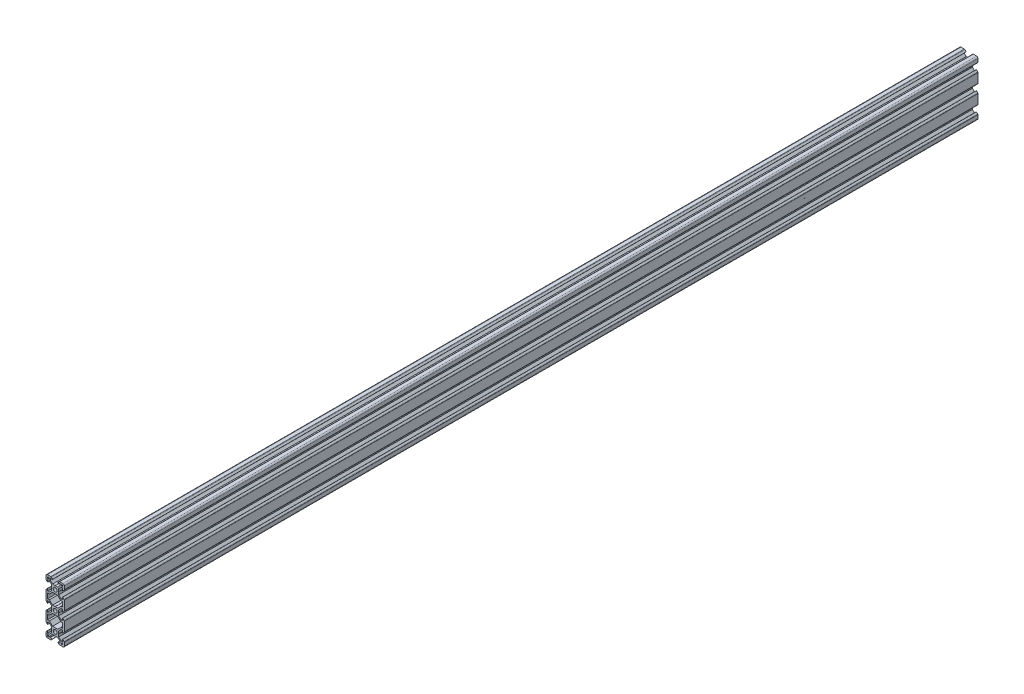
SolidWorks part; units mm, degrees
ref_plane "Front Plane" through (0, 0, 0) normal (0, 0, 1) x (1, 0, 0)
ref_plane "Top Plane" through (0, 0, 0) normal (0, 1, 0) x (1, 0, 0)
ref_plane "Right Plane" through (0, 0, 0) normal (1, 0, 0) x (0, 0, -1)
sketch "Sketch2" plane through (0, 0, 0) normal (0, 0, 1) x (1, 0, 0)
  line L0 (-8.2, 2.8875) -> (-8.2, 5.4975)
  line L3 (-4.9072, 9.9975) -> (-8.5, 9.9975)
  line L4 (-10, 4.9047) -> (-10, 8.4975)
  line L5 (-2.1, 0) -> (-3.8, 0) construction
  line L6 (0, 3.8) -> (0, 2.1) construction
  line L7 (-0.1, 3.9) -> (-2.8404, 3.9)
  line L8 (-3.9, 0.1) -> (-3.9, 2.8383)
  line L9 (-2.89, 8.1975) -> (-5.5, 8.1975)
  line L10 (-6.57, 8.1975) -> (-6.57, 7.6575)
  line L11 (-8.2, 6.5675) -> (-7.66, 6.5675)
  line L12 (-5.5, 8.1975) -> (-5.5, 6.5588)
  line L13 (-6.56, 5.4975) -> (-8.2, 5.4975)
  line L14 (-8.2, 8.1975) -> (-1.4852, 1.4847) construction
  line L15 (-6.56, 5.4975) -> (-3.9, 2.8383)
  line L16 (-5.5, 6.5588) -> (-2.8404, 3.9)
  line L17 (-7.66, 6.5675) -> (-6.57, 7.6575)
  line L18 (-8.7302, 7.6671) -> (-0.5302, -0.5304) construction
  line L19 (-7.6698, 8.7279) -> (0.5302, 0.5304) construction
  line L20 (-8.2, 8.1975) -> (0, 0) construction
  line L21 (-8.2, 6.5675) -> (-8.2, 8.1975)
  line L22 (-8.2, -0.0025) -> (-8.2, 8.1975) construction
  line L23 (-6.57, 8.1975) -> (-8.2, 8.1975)
  line L24 (0, 8.1975) -> (-8.2, 8.1975) construction
  line L25 (-10, -0.0025) -> (-10, 9.9975) construction
  line L26 (0, 9.9975) -> (-10, 9.9975) construction
  line L27 (-2.89, 8.3075) -> (-2.89, 8.1975)
  line L29 (-8.31, 2.8875) -> (-8.2, 2.8875)
  line L30 (-4.3486, 9.7661) -> (-2.89, 8.3075)
  line L31 (-8.31, 2.8875) -> (-9.7686, 4.3461)
  line L34 (-0.1, 3.9) -> (0, 3.8)
  line L35 (-3.9, 0.1) -> (-3.8, 0)
  line L36 (-10, -20) -> (0, -20) construction
  line L37 (0, 0) -> (0, -20) construction
  line L38 (0, -3.9) -> (-2.8404, -3.9)
  line L39 (-3.8, 0) -> (-3.9, -0.1)
  line L40 (-3.9, -0.1) -> (-3.9, -2.84)
  line L41 (-2.8404, -3.9) -> (-6.25, -7.3096)
  line L42 (-3.9, -2.84) -> (-6.56, -5.5)
  line L43 (-8.21, -2.89) -> (-8.21, -5.5)
  line L44 (-6.56, 5.4975) -> (-6.56, -5.5) construction
  line L45 (-6.56, -5.5) -> (-8.21, -5.5)
  line L46 (-6.25, -7.3096) -> (-6.25, -12.7) construction
  line L47 (-6.25, -7.3096) -> (-8.21, -7.3096)
  line L48 (-8.21, -2.89) -> (-8.31, -2.89)
  line L49 (-8.31, -2.89) -> (-9.7657, -4.3457)
  line L51 (-8.21, -7.3096) -> (-8.21, -12.7)
  line L52 (-0.1, -16.1) -> (-2.85, -16.1)
  line L53 (-3.9, -17.16) -> (-3.9, -19.9)
  line L54 (-6.25, -12.7) -> (-2.85, -16.1)
  line L58 (-3.9, -17.16) -> (-6.56, -14.5)
  line L60 (-8.21, -17.11) -> (-8.31, -17.11)
  line L61 (-10, -4.9114) -> (-10, -15.0886)
  line L62 (-9.7657, -15.6543) -> (-8.31, -17.11)
  line L63 (-0.1, -16.1) -> (0, -16.2)
  line L64 (-3.9, -19.9) -> (-3.8, -20)
  line L65 (-8.21, -14.5) -> (-6.56, -14.5)
  line L66 (-8.21, -12.7) -> (-6.25, -12.7)
  line L68 (-8.21, -14.5) -> (-8.21, -17.11)
  arc A1 (-10, 8.4975) -> (-8.5, 9.9975) centre (-8.5, 8.4975) cw
  arc A2 (-9.7686, 4.3461) -> (-10, 4.9047) centre (-9.21, 4.9047) cw
  arc A3 (-4.3486, 9.7661) -> (-4.9072, 9.9975) centre (-4.9072, 9.2075) ccw
  arc A4 (-2.1, -20) -> (0, -17.9) centre (0, -20) cw
  arc A5 (0, 2.1) -> (0, -2.1) centre (0, 0) ccw
  arc A6 (-9.7657, -15.6543) -> (-10, -15.0886) centre (-9.2, -15.0886) cw
  arc A7 (-9.7657, -4.3457) -> (-10, -4.9114) centre (-9.2, -4.9114) ccw
  point P29 (-10, 9.9975)
  point P39 (-10, 4.5775)
  point P42 (-4.58, 9.9975)
  point P76 (-10, -15.42)
  point P79 (-10, -4.58)
  dimension "D15" = 1.5
  dimension "D22" = 0.79
  dimension "D30" = 2.1
  dimension "D31" = 2.1
  dimension "D51" = 0.8
  dimension "D4" = 1.8
  dimension "D5" = 3.43
  dimension "D6" = 3.43
  dimension "D7" = 0.54
  dimension "D8" = 0.54
  dimension "D9" = 1.07
  dimension "D10" = 1.07
  dimension "D11" = 3.9
  dimension "D12" = 3.9
  dimension "D16" = 7.11
  dimension "D17" = 0.11
  dimension "D18" = 1.69
  dimension "D19" = 0.11
  dimension "D20" = 7.11
  dimension "D21" = 1.69
  dimension "D23" = 10
  dimension "D24" = 0.1
  dimension "D25" = 45
  dimension "D26" = 0.1
  dimension "D27" = 45
  dimension "D28" = 1.64
  dimension "D29" = 20
  dimension "D32" = 3.9
  dimension "D33" = 45
  dimension "D34" = 2.74
  dimension "D35" = 45
  dimension "D36" = 1.96
  dimension "D37" = 2.61
  dimension "D38" = 90
  dimension "D39" = 2.61
  dimension "D40" = 3.9
  dimension "D41" = 3.9
  dimension "D42" = 135
  dimension "D44" = 45
  dimension "D45" = 1.8
  dimension "D46" = 0.1
  dimension "D47" = 0.1
  dimension "D48" = 45
  dimension "D49" = 0.1
  dimension "D50" = 45
  dimension "D43" = 5.5
  dimension "D13" = 0.75
  dimension "D14" = 0.75
sketch "Sketch6" plane through (0, 0, 0) normal (0, 0, 1) x (1, 0, 0)
  line L0 (-0.1, 3.9) -> (0, 3.8) construction
  line L1 (-0.1, 3.9) -> (-2.8404, 3.9) construction
  line L2 (-5.5, 6.5588) -> (-2.8404, 3.9) construction
  line L3 (-5.5, 8.1975) -> (-5.5, 6.5588) construction
  line L4 (-2.89, 8.1975) -> (-5.5, 8.1975) construction
  line L5 (-7.66, 6.5675) -> (-6.57, 7.6575)
  line L6 (-6.57, 7.6575) -> (-6.57, 8.1975)
  line L7 (-6.57, 8.1975) -> (-8.2, 8.1975)
  line L8 (-8.2, 8.1975) -> (-8.2, 6.5675)
  line L9 (-8.2, 6.5675) -> (-7.66, 6.5675)
  line L10 (-7.66, 6.5675) -> (-6.57, 7.6575)
  line L11 (-6.57, 7.6575) -> (-6.57, 8.1975)
  line L12 (-6.57, 8.1975) -> (-8.2, 8.1975)
  line L13 (-8.2, 8.1975) -> (-8.2, 6.5675)
  line L14 (-8.2, 6.5675) -> (-7.66, 6.5675)
  line L15 (-2.89, 8.3075) -> (-2.89, 8.1975) construction
  line L16 (-4.3486, 9.7661) -> (-2.89, 8.3075) construction
  line L17 (-4.9072, 9.9975) -> (-8.5, 9.9975) construction
  line L18 (-10, 4.9047) -> (-10, 8.4975) construction
  line L19 (-8.31, 2.8875) -> (-9.7686, 4.3461) construction
  line L20 (-8.31, 2.8875) -> (-8.2, 2.8875) construction
  line L21 (-8.2, 2.8875) -> (-8.2, 5.4975) construction
  line L22 (-6.56, 5.4975) -> (-8.2, 5.4975) construction
  line L23 (-6.56, 5.4975) -> (-3.9, 2.8383) construction
  line L24 (-3.9, 0.1) -> (-3.9, 2.8383) construction
  line L25 (-3.9, 0.1) -> (-3.8, 0) construction
  line L26 (-3.8, 0) -> (-3.9, -0.1) construction
  line L27 (-3.9, -0.1) -> (-3.9, -2.84) construction
  line L28 (-3.9, -2.84) -> (-6.56, -5.5) construction
  line L29 (-6.56, -5.5) -> (-8.21, -5.5) construction
  line L30 (-8.21, -2.89) -> (-8.21, -5.5) construction
  line L31 (-8.21, -2.89) -> (-8.31, -2.89) construction
  line L32 (-8.31, -2.89) -> (-9.7657, -4.3457) construction
  line L33 (-10, -4.9114) -> (-10, -15.0886) construction
  line L34 (-9.7657, -15.6543) -> (-8.31, -17.11) construction
  line L35 (-8.21, -17.11) -> (-8.31, -17.11) construction
  line L36 (-8.21, -14.5) -> (-8.21, -17.11) construction
  line L37 (-8.21, -14.5) -> (-6.56, -14.5) construction
  line L38 (-3.9, -17.16) -> (-6.56, -14.5) construction
  line L39 (-3.9, -17.16) -> (-3.9, -19.9) construction
  line L40 (-3.9, -19.9) -> (-3.8, -20) construction
  line L41 (0, -3.9) -> (-2.8404, -3.9) construction
  line L42 (-2.8404, -3.9) -> (-6.25, -7.3096) construction
  line L43 (-6.25, -7.3096) -> (-8.21, -7.3096) construction
  line L44 (-8.21, -7.3096) -> (-8.21, -12.7) construction
  line L45 (-8.21, -12.7) -> (-6.25, -12.7) construction
  line L46 (-6.25, -12.7) -> (-2.85, -16.1) construction
  line L47 (-0.1, -16.1) -> (-2.85, -16.1) construction
  line L48 (-0.1, -16.1) -> (0, -16.2) construction
  line L49 (-0.1, 3.9) -> (0, 3.8)
  line L50 (-0.1, 3.9) -> (-2.8404, 3.9)
  line L51 (-5.5, 6.5588) -> (-2.8404, 3.9)
  line L52 (-5.5, 8.1975) -> (-5.5, 6.5588)
  line L53 (-2.89, 8.1975) -> (-5.5, 8.1975)
  line L54 (-2.89, 8.3075) -> (-2.89, 8.1975)
  line L55 (-4.3486, 9.7661) -> (-2.89, 8.3075)
  line L56 (-4.9072, 9.9975) -> (-8.5, 9.9975)
  line L57 (-10, 4.9047) -> (-10, 8.4975)
  line L58 (-8.31, 2.8875) -> (-9.7686, 4.3461)
  line L59 (-8.31, 2.8875) -> (-8.2, 2.8875)
  line L60 (-8.2, 2.8875) -> (-8.2, 5.4975)
  line L61 (-6.56, 5.4975) -> (-8.2, 5.4975)
  line L62 (-6.56, 5.4975) -> (-3.9, 2.8383)
  line L63 (-3.9, 0.1) -> (-3.9, 2.8383)
  line L64 (-3.9, 0.1) -> (-3.8, 0)
  line L65 (-3.8, 0) -> (-3.9, -0.1)
  line L66 (-3.9, -0.1) -> (-3.9, -2.84)
  line L67 (-3.9, -2.84) -> (-6.56, -5.5)
  line L68 (-6.56, -5.5) -> (-8.21, -5.5)
  line L69 (-8.21, -2.89) -> (-8.21, -5.5)
  line L70 (-8.21, -2.89) -> (-8.31, -2.89)
  line L71 (-8.31, -2.89) -> (-9.7657, -4.3457)
  line L72 (-10, -4.9114) -> (-10, -15.0886)
  line L73 (-9.7657, -15.6543) -> (-8.31, -17.11)
  line L74 (-8.21, -17.11) -> (-8.31, -17.11)
  line L75 (-8.21, -14.5) -> (-8.21, -17.11)
  line L76 (-8.21, -14.5) -> (-6.56, -14.5)
  line L77 (-3.9, -17.16) -> (-6.56, -14.5)
  line L78 (-3.9, -17.16) -> (-3.9, -19.9)
  line L79 (-3.9, -19.9) -> (-3.8, -20)
  line L80 (2.8404, -3.9) -> (-2.8404, -3.9)
  line L81 (-2.8404, -3.9) -> (-6.25, -7.3096)
  line L82 (-6.25, -7.3096) -> (-8.21, -7.3096)
  line L83 (-8.21, -7.3096) -> (-8.21, -12.7)
  line L84 (-8.21, -12.7) -> (-6.25, -12.7)
  line L85 (-6.25, -12.7) -> (-2.85, -16.1)
  line L86 (-0.1, -16.1) -> (-2.85, -16.1)
  line L87 (-0.1, -16.1) -> (0, -16.2)
  line L88 (0, 9.9975) -> (0, -49.9975) construction
  line L89 (-10, -20) -> (10, -20) construction
  line L90 (0.1, -16.1) -> (0, -16.2)
  line L91 (0.1, -16.1) -> (2.85, -16.1)
  line L92 (6.25, -12.7) -> (2.85, -16.1)
  line L93 (8.21, -12.7) -> (6.25, -12.7)
  line L94 (8.21, -7.3096) -> (8.21, -12.7)
  line L95 (6.25, -7.3096) -> (8.21, -7.3096)
  line L96 (2.8404, -3.9) -> (6.25, -7.3096)
  line L97 (3.9, -19.9) -> (3.8, -20)
  line L98 (3.9, -17.16) -> (3.9, -19.9)
  line L99 (3.9, -17.16) -> (6.56, -14.5)
  line L100 (8.21, -14.5) -> (6.56, -14.5)
  line L101 (8.21, -14.5) -> (8.21, -17.11)
  line L102 (8.21, -17.11) -> (8.31, -17.11)
  line L103 (9.7657, -15.6543) -> (8.31, -17.11)
  line L104 (10, -4.9114) -> (10, -15.0886)
  line L105 (8.31, -2.89) -> (9.7657, -4.3457)
  line L106 (8.21, -2.89) -> (8.31, -2.89)
  line L107 (8.21, -2.89) -> (8.21, -5.5)
  line L108 (6.56, -5.5) -> (8.21, -5.5)
  line L109 (3.9, -2.84) -> (6.56, -5.5)
  line L110 (3.9, -0.1) -> (3.9, -2.84)
  line L111 (3.8, 0) -> (3.9, -0.1)
  line L112 (3.9, 0.1) -> (3.8, 0)
  line L113 (3.9, 0.1) -> (3.9, 2.8383)
  line L114 (6.56, 5.4975) -> (3.9, 2.8383)
  line L115 (6.56, 5.4975) -> (8.2, 5.4975)
  line L116 (8.2, 2.8875) -> (8.2, 5.4975)
  line L117 (8.31, 2.8875) -> (8.2, 2.8875)
  line L118 (8.31, 2.8875) -> (9.7686, 4.3461)
  line L119 (10, 4.9047) -> (10, 8.4975)
  line L120 (4.9072, 9.9975) -> (8.5, 9.9975)
  line L121 (4.3486, 9.7661) -> (2.89, 8.3075)
  line L122 (2.89, 8.3075) -> (2.89, 8.1975)
  line L123 (2.89, 8.1975) -> (5.5, 8.1975)
  line L124 (5.5, 8.1975) -> (5.5, 6.5588)
  line L125 (5.5, 6.5588) -> (2.8404, 3.9)
  line L126 (0.1, 3.9) -> (2.8404, 3.9)
  line L127 (0.1, 3.9) -> (0, 3.8)
  line L128 (8.2, 6.5675) -> (7.66, 6.5675)
  line L129 (8.2, 8.1975) -> (8.2, 6.5675)
  line L130 (6.57, 8.1975) -> (8.2, 8.1975)
  line L131 (6.57, 7.6575) -> (6.57, 8.1975)
  line L132 (7.66, 6.5675) -> (6.57, 7.6575)
  line L133 (7.66, -46.5675) -> (6.57, -47.6575)
  line L134 (6.57, -47.6575) -> (6.57, -48.1975)
  line L135 (6.57, -48.1975) -> (8.2, -48.1975)
  line L136 (8.2, -48.1975) -> (8.2, -46.5675)
  line L137 (8.2, -46.5675) -> (7.66, -46.5675)
  line L138 (0.1, -43.9) -> (0, -43.8)
  line L139 (0.1, -43.9) -> (2.8404, -43.9)
  line L140 (5.5, -46.5588) -> (2.8404, -43.9)
  line L141 (5.5, -48.1975) -> (5.5, -46.5588)
  line L142 (2.89, -48.1975) -> (5.5, -48.1975)
  line L143 (2.89, -48.3075) -> (2.89, -48.1975)
  line L144 (4.3486, -49.7661) -> (2.89, -48.3075)
  line L145 (4.9072, -49.9975) -> (8.5, -49.9975)
  line L146 (10, -44.9047) -> (10, -48.4975)
  line L147 (8.31, -42.8875) -> (9.7686, -44.3461)
  line L148 (8.31, -42.8875) -> (8.2, -42.8875)
  line L149 (8.2, -42.8875) -> (8.2, -45.4975)
  line L150 (6.56, -45.4975) -> (8.2, -45.4975)
  line L151 (6.56, -45.4975) -> (3.9, -42.8383)
  line L152 (3.9, -40.1) -> (3.9, -42.8383)
  line L153 (3.9, -40.1) -> (3.8, -40)
  line L154 (3.8, -40) -> (3.9, -39.9)
  line L155 (3.9, -39.9) -> (3.9, -37.16)
  line L156 (3.9, -37.16) -> (6.56, -34.5)
  line L157 (6.56, -34.5) -> (8.21, -34.5)
  line L158 (8.21, -37.11) -> (8.21, -34.5)
  line L159 (8.21, -37.11) -> (8.31, -37.11)
  line L160 (8.31, -37.11) -> (9.7657, -35.6543)
  line L161 (10, -35.0886) -> (10, -24.9114)
  line L162 (9.7657, -24.3457) -> (8.31, -22.89)
  line L163 (8.21, -22.89) -> (8.31, -22.89)
  line L164 (8.21, -25.5) -> (8.21, -22.89)
  line L165 (8.21, -25.5) -> (6.56, -25.5)
  line L166 (3.9, -22.84) -> (6.56, -25.5)
  line L167 (3.9, -22.84) -> (3.9, -20.1)
  line L168 (3.9, -20.1) -> (3.8, -20)
  line L169 (2.8404, -36.1) -> (6.25, -32.6904)
  line L170 (6.25, -32.6904) -> (8.21, -32.6904)
  line L171 (8.21, -32.6904) -> (8.21, -27.3)
  line L172 (8.21, -27.3) -> (6.25, -27.3)
  line L173 (6.25, -27.3) -> (2.85, -23.9)
  line L174 (0.1, -23.9) -> (2.85, -23.9)
  line L175 (0.1, -23.9) -> (0, -23.8)
  line L176 (-0.1, -23.9) -> (0, -23.8)
  line L177 (-0.1, -23.9) -> (-2.85, -23.9)
  line L178 (-6.25, -27.3) -> (-2.85, -23.9)
  line L179 (-8.21, -27.3) -> (-6.25, -27.3)
  line L180 (-8.21, -32.6904) -> (-8.21, -27.3)
  line L181 (-6.25, -32.6904) -> (-8.21, -32.6904)
  line L182 (-2.8404, -36.1) -> (-6.25, -32.6904)
  line L183 (2.8404, -36.1) -> (-2.8404, -36.1)
  line L184 (-3.9, -20.1) -> (-3.8, -20)
  line L185 (-3.9, -22.84) -> (-3.9, -20.1)
  line L186 (-3.9, -22.84) -> (-6.56, -25.5)
  line L187 (-8.21, -25.5) -> (-6.56, -25.5)
  line L188 (-8.21, -25.5) -> (-8.21, -22.89)
  line L189 (-8.21, -22.89) -> (-8.31, -22.89)
  line L190 (-9.7657, -24.3457) -> (-8.31, -22.89)
  line L191 (-10, -35.0886) -> (-10, -24.9114)
  line L192 (-8.31, -37.11) -> (-9.7657, -35.6543)
  line L193 (-8.21, -37.11) -> (-8.31, -37.11)
  line L194 (-8.21, -37.11) -> (-8.21, -34.5)
  line L195 (-6.56, -34.5) -> (-8.21, -34.5)
  line L196 (-3.9, -37.16) -> (-6.56, -34.5)
  line L197 (-3.9, -39.9) -> (-3.9, -37.16)
  line L198 (-3.8, -40) -> (-3.9, -39.9)
  line L199 (-3.9, -40.1) -> (-3.8, -40)
  line L200 (-3.9, -40.1) -> (-3.9, -42.8383)
  line L201 (-6.56, -45.4975) -> (-3.9, -42.8383)
  line L202 (-6.56, -45.4975) -> (-8.2, -45.4975)
  line L203 (-8.2, -42.8875) -> (-8.2, -45.4975)
  line L204 (-8.31, -42.8875) -> (-8.2, -42.8875)
  line L205 (-8.31, -42.8875) -> (-9.7686, -44.3461)
  line L206 (-10, -44.9047) -> (-10, -48.4975)
  line L207 (-4.9072, -49.9975) -> (-8.5, -49.9975)
  line L208 (-4.3486, -49.7661) -> (-2.89, -48.3075)
  line L209 (-2.89, -48.3075) -> (-2.89, -48.1975)
  line L210 (-2.89, -48.1975) -> (-5.5, -48.1975)
  line L211 (-5.5, -48.1975) -> (-5.5, -46.5588)
  line L212 (-5.5, -46.5588) -> (-2.8404, -43.9)
  line L213 (-0.1, -43.9) -> (-2.8404, -43.9)
  line L214 (-0.1, -43.9) -> (0, -43.8)
  line L215 (-8.2, -46.5675) -> (-7.66, -46.5675)
  line L216 (-8.2, -48.1975) -> (-8.2, -46.5675)
  line L217 (-6.57, -48.1975) -> (-8.2, -48.1975)
  line L218 (-6.57, -47.6575) -> (-6.57, -48.1975)
  line L219 (-7.66, -46.5675) -> (-6.57, -47.6575)
  arc A0 (0, 2.1) -> (0, -2.1) centre (0, 0) ccw construction
  arc A1 (0, -17.9) -> (-2.1, -20) centre (0, -20) ccw construction
  arc A2 (-4.3486, 9.7661) -> (-4.9072, 9.9975) centre (-4.9072, 9.2075) ccw construction
  arc A3 (-8.5, 9.9975) -> (-10, 8.4975) centre (-8.5, 8.4975) ccw construction
  arc A4 (-10, 4.9047) -> (-9.7686, 4.3461) centre (-9.21, 4.9047) ccw construction
  arc A5 (-9.7657, -4.3457) -> (-10, -4.9114) centre (-9.2, -4.9114) ccw construction
  arc A6 (-10, -15.0886) -> (-9.7657, -15.6543) centre (-9.2, -15.0886) ccw construction
  circle A7 centre (0, 0) radius 2.1
  circle A8 centre (0, -20) radius 2.1
  arc A9 (-4.3486, 9.7661) -> (-4.9072, 9.9975) centre (-4.9072, 9.2075) ccw
  arc A10 (-8.5, 9.9975) -> (-10, 8.4975) centre (-8.5, 8.4975) ccw
  arc A11 (-10, 4.9047) -> (-9.7686, 4.3461) centre (-9.21, 4.9047) ccw
  arc A12 (-9.7657, -4.3457) -> (-10, -4.9114) centre (-9.2, -4.9114) ccw
  arc A13 (-10, -15.0886) -> (-9.7657, -15.6543) centre (-9.2, -15.0886) ccw
  arc A14 (10, -15.0886) -> (9.7657, -15.6543) centre (9.2, -15.0886) cw
  arc A15 (9.7657, -4.3457) -> (10, -4.9114) centre (9.2, -4.9114) cw
  arc A16 (10, 4.9047) -> (9.7686, 4.3461) centre (9.21, 4.9047) cw
  arc A17 (8.5, 9.9975) -> (10, 8.4975) centre (8.5, 8.4975) cw
  arc A18 (4.3486, 9.7661) -> (4.9072, 9.9975) centre (4.9072, 9.2075) cw
  arc A19 (4.3486, -49.7661) -> (4.9072, -49.9975) centre (4.9072, -49.2075) ccw
  arc A20 (8.5, -49.9975) -> (10, -48.4975) centre (8.5, -48.4975) ccw
  arc A21 (10, -44.9047) -> (9.7686, -44.3461) centre (9.21, -44.9047) ccw
  arc A22 (9.7657, -35.6543) -> (10, -35.0886) centre (9.2, -35.0886) ccw
  arc A23 (10, -24.9114) -> (9.7657, -24.3457) centre (9.2, -24.9114) ccw
  arc A24 (-10, -24.9114) -> (-9.7657, -24.3457) centre (-9.2, -24.9114) cw
  arc A25 (-9.7657, -35.6543) -> (-10, -35.0886) centre (-9.2, -35.0886) cw
  arc A26 (-10, -44.9047) -> (-9.7686, -44.3461) centre (-9.21, -44.9047) cw
  arc A27 (-8.5, -49.9975) -> (-10, -48.4975) centre (-8.5, -48.4975) cw
  arc A28 (-4.3486, -49.7661) -> (-4.9072, -49.9975) centre (-4.9072, -49.2075) cw
  circle A29 centre (0, -40) radius 2.1
  dimension "D1" = 0
extrude "Boss-Extrude1" add sketch "Sketch6" against normal blind 1000
